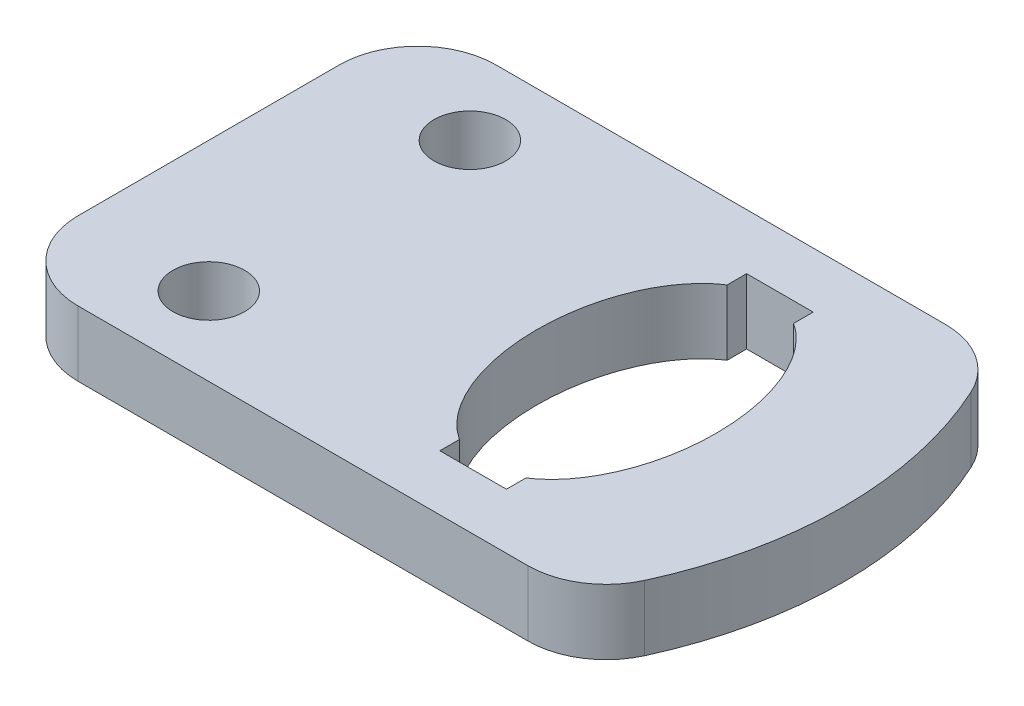
SolidWorks part; units mm, degrees
ref_plane "Front Plane" through (0, 0, 0) normal (0, 0, 1) x (1, 0, 0)
ref_plane "Top Plane" through (0, 0, 0) normal (0, 1, 0) x (1, 0, 0)
ref_plane "Right Plane" through (0, 0, 0) normal (1, 0, 0) x (0, 0, -1)
sketch "Sketch1" plane through (0, 0, 0) normal (0, 0, 1) x (1, 0, 0)
  line L3 (0, -5) -> (44, -5)
  line L4 (44, -5) -> (44, 0)
  line L5 (44, 0) -> (0, 0)
  line L9 (0, 0) -> (0, -5)
  dimension "D2" = 5
  dimension "D1" = 44
extrude "Boss-Extrude1" add sketch "Sketch1" along normal blind 32
sketch "Sketch2" plane through (0, -5, 0) normal (0, -1, 0) x (1, 0, 0)
  line L0 (29.45, 5.75) -> (29.45, 4.25)
  line L1 (29.45, 27.75) -> (34.55, 27.75)
  line L2 (29.45, 27.75) -> (29.45, 26.25)
  line L3 (29.45, 4.25) -> (34.55, 4.25)
  line L4 (34.55, 27.75) -> (34.55, 26.25)
  line L5 (34.55, 5.75) -> (34.55, 4.25)
  line L6 (32, 16) -> (0, 16) construction
  line L9 (44, 32) -> (44, 0) construction
  line L10 (0, 32) -> (0, 0) construction
  circle A0 centre (10, 26) radius 2.75
  circle A1 centre (10, 6) radius 2.75
  ellipse E0 centre (32, 16) end of major axis (32, 27.0373) minor radius 6.875 (29.45, 26.25) -> (29.45, 5.75) ccw
  ellipse E1 centre (32, 16) end of major axis (32, 27.0373) minor radius 6.875 (34.55, 5.75) -> (34.55, 26.25) ccw
  dimension "D8" = 5.5
  dimension "D1" = 5.1
  dimension "D2" = 23.5
  dimension "D3" = 20.5
  dimension "D4" = 13.75
  dimension "D5" = 12
  dimension "D6" = 10
  dimension "D7" = 20
  dimension "D9" = 10
extrude "Cut-Extrude1" cut sketch "Sketch2" against normal through all
sketch "Sketch3" plane through (0, -5, 0) normal (0, -1, 0) x (1, 0, 0)
  line L0 (44, 32) -> (44, 0) construction
  line L1 (44, 32) -> (44, 0)
  arc A0 (44, 0) -> (44, 32) centre (18.6228, 16) ccw
  dimension "D1" = 30
extrude "Boss-Extrude2" add sketch "Sketch3" against normal up to surface (5 mm away) up to face at (12.75, 0, 6)
fillet "Fillet1" radius 6 4 edges at (0, -2.5, 0) (0, -2.5, 32) (44, -2.5, 0) (44, -2.5, 32)
